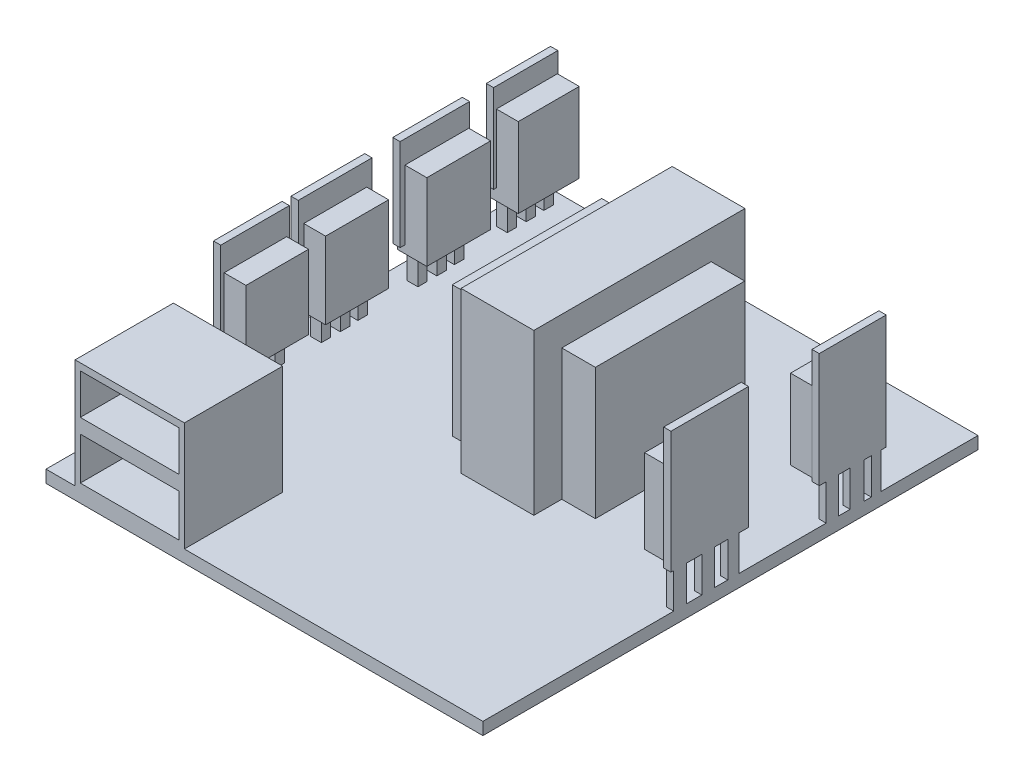
SolidWorks part; units mm, degrees
ref_plane "Front Plane" through (0, 0, 0) normal (0, 0, 1) x (1, 0, 0)
ref_plane "Top Plane" through (0, 0, 0) normal (0, 1, 0) x (1, 0, 0)
ref_plane "Right Plane" through (0, 0, 0) normal (1, 0, 0) x (0, 0, -1)
sketch "Sketch1" plane through (0, 0, 0) normal (0, 1, 0) x (1, 0, 0)
  line L1 (-32.4342, 13.5526) -> (27.5658, 13.5526)
  line L2 (-32.4342, 13.5526) -> (-32.4342, -54.4474)
  line L3 (-32.4342, -54.4474) -> (27.5658, -54.4474)
  line L4 (27.5658, 13.5526) -> (27.5658, -54.4474)
  dimension "D1" = 60
  dimension "D2" = 68
extrude "Boss-Extrude1" add sketch "Sketch1" along normal blind 1.7
sketch "Sketch2" plane through (0, 1.7, 0) normal (0, 1, 0) x (1, 0, 0)
  line L0 (27.5658, -54.4474) -> (27.5658, 13.5526) construction
  line L1 (-3.4342, 2.5526) -> (6.5658, 2.5526)
  line L2 (-3.4342, 2.5526) -> (-3.4342, -26.4474)
  line L3 (-3.4342, -26.4474) -> (6.5658, -26.4474)
  line L4 (6.5658, 2.5526) -> (6.5658, -26.4474)
  line L5 (-32.4342, -54.4474) -> (27.5658, -54.4474) construction
  dimension "D1" = 29
  dimension "D2" = 10
  dimension "D3" = 21
  dimension "D4" = 28
extrude "Boss-Extrude2" add sketch "Sketch2" along normal blind 22
sketch "Sketch3" plane through (0, 1.7, 0) normal (0, 1, 0) x (1, 0, 0)
  line L1 (-8.4662, -2.0985) -> (11.1829, -2.0985)
  line L2 (-8.4662, -2.0985) -> (-8.4662, -22.6146)
  line L3 (-8.4662, -22.6146) -> (11.1829, -22.6146)
  line L4 (11.1829, -2.0985) -> (11.1829, -22.6146)
extrude "Boss-Extrude3" add sketch "Sketch3" along normal blind 18
sketch "Sketch4" plane through (0, 1.7, 0) normal (0, 1, 0) x (1, 0, 0)
  line L0 (-32.4342, -54.4474) -> (27.5658, -54.4474) construction
  line L1 (-28.4342, -40.9474) -> (-13.4342, -40.9474)
  line L2 (-28.4342, -40.9474) -> (-28.4342, -54.4474)
  line L3 (-28.4342, -54.4474) -> (-13.4342, -54.4474)
  line L4 (-13.4342, -40.9474) -> (-13.4342, -54.4474)
  line L5 (-32.4342, 13.5526) -> (-32.4342, -54.4474) construction
  dimension "D1" = 15
  dimension "D2" = 13.5
  dimension "D3" = 4
extrude "Boss-Extrude4" add sketch "Sketch4" along normal blind 15
sketch "Sketch5" plane through (0, 0, 54.4474) normal (0, 0, 1) x (1, 0, 0)
  line L1 (-27.7262, 15.7476) -> (-14.1813, 15.7476)
  line L2 (-27.7262, 15.7476) -> (-27.7262, 10.2076)
  line L3 (-27.7262, 10.2076) -> (-14.1813, 10.2076)
  line L4 (-14.1813, 15.7476) -> (-14.1813, 10.2076)
  line L5 (-27.7262, 8.2207) -> (-14.1813, 8.2207)
  line L6 (-27.7262, 8.2207) -> (-27.7262, 2.3932)
  line L7 (-27.7262, 2.3932) -> (-14.1813, 2.3932)
  line L8 (-14.1813, 8.2207) -> (-14.1813, 2.3932)
extrude "Cut-Extrude2" cut sketch "Sketch5" against normal blind 13
sketch "Sketch6" plane through (27.5658, 0, 0) normal (1, 0, 0) x (0, 0, -1)
  line L1 (-28.2345, 18.5486) -> (-18.4099, 18.5486)
  line L2 (-28.2345, 18.5486) -> (-28.2345, 7.0494)
  line L3 (-28.2345, 7.0494) -> (-18.4099, 7.0494)
  line L4 (-18.4099, 18.5486) -> (-18.4099, 7.0494)
  line L5 (-8.1946, 17.9904) -> (0.9043, 17.9904)
  line L6 (-8.1946, 17.9904) -> (-8.1946, 7.0494)
  line L7 (-8.1946, 7.0494) -> (0.9043, 7.0494)
  line L8 (0.9043, 17.9904) -> (0.9043, 7.0494)
extrude "Boss-Extrude5" add sketch "Sketch6" against normal blind 4 separate body
sketch "Sketch7" plane through (27.5658, 0, 0) normal (1, 0, 0) x (0, 0, -1)
  line L0 (-28.2345, 18.5486) -> (-28.2345, 7.0494) construction
  line L1 (-28.2345, 8.6124) -> (-26.4474, 8.6124)
  line L2 (-28.2345, 8.6124) -> (-28.2345, 1.7)
  line L3 (-28.2345, 1.7) -> (-26.4474, 1.7)
  line L4 (-26.4474, 8.6124) -> (-26.4474, 1.7)
  line L5 (-22.6146, 1.7) -> (-2.0985, 1.7) construction
  line L6 (-24.3828, 8.6124) -> (-22.6146, 8.6124)
  line L7 (-24.3828, 8.6124) -> (-24.3828, 1.7)
  line L8 (-24.3828, 1.7) -> (-22.6146, 1.7)
  line L9 (-22.6146, 8.6124) -> (-22.6146, 1.7)
  line L10 (-20.8102, 8.6124) -> (-19.303, 8.6124)
  line L11 (-20.8102, 8.6124) -> (-20.8102, 1.7)
  line L12 (-20.8102, 1.7) -> (-19.303, 1.7)
  line L13 (-19.303, 8.6124) -> (-19.303, 1.7)
  line L14 (-54.4474, 1.7) -> (13.5526, 1.7) construction
  line L15 (-7.3014, 8.1658) -> (-5.6268, 8.1658)
  line L16 (-7.3014, 8.1658) -> (-7.3014, 1.7)
  line L17 (-7.3014, 1.7) -> (-5.6268, 1.7)
  line L18 (-5.6268, 8.1658) -> (-5.6268, 1.7)
  line L19 (-4.008, 8.1658) -> (-2.0985, 8.1658)
  line L20 (-4.008, 8.1658) -> (-4.008, 1.7)
  line L21 (-4.008, 1.7) -> (-2.0985, 1.7)
  line L22 (-2.0985, 8.1658) -> (-2.0985, 1.7)
  line L23 (-2.0985, 1.7) -> (2.5526, 1.7) construction
  line L24 (-1.1052, 8.1658) -> (0.227, 8.1658)
  line L25 (-1.1052, 8.1658) -> (-1.1052, 1.7)
  line L26 (-1.1052, 1.7) -> (0.227, 1.7)
  line L27 (0.227, 8.1658) -> (0.227, 1.7)
extrude "Boss-Extrude6" add sketch "Sketch7" against normal blind 1
sketch "Sketch8" plane through (27.5658, 0, 0) normal (1, 0, 0) x (0, 0, -1)
  line L1 (-17.9644, 6.5308) -> (-28.6207, 6.5308)
  line L2 (-17.9644, 6.5308) -> (-17.9644, 23.2934)
  line L3 (-17.9644, 23.2934) -> (-28.6207, 23.2934)
  line L4 (-28.6207, 6.5308) -> (-28.6207, 23.2934)
  line L5 (0.939, 6.6234) -> (-8.2504, 6.6234)
  line L6 (0.939, 6.6234) -> (0.939, 22.3444)
  line L7 (0.939, 22.3444) -> (-8.2504, 22.3444)
  line L8 (-8.2504, 6.6234) -> (-8.2504, 22.3444)
  point P10 (-17.9644, 6.5308)
  point P11 (0, 0)
  point P12 (0.939, 6.6234)
extrude "Boss-Extrude7" add sketch "Sketch8" against normal blind 1
sketch "Sketch9" plane through (0, 1.7, 0) normal (0, 1, 0) x (1, 0, 0)
  line L0 (-30.0284, -0.7621) -> (-28.707, -0.7621)
  line L1 (-30.3316, 11.821) -> (-29.0103, 11.821)
  line L2 (-30.3316, 11.821) -> (-30.3316, 10.4996)
  line L3 (-30.3316, 10.4996) -> (-29.0103, 10.4996)
  line L4 (-29.0103, 11.821) -> (-29.0103, 10.4996)
  line L5 (-30.3981, 9.2559) -> (-28.881, 9.2559)
  line L6 (-30.3981, 9.2559) -> (-30.3981, 7.9556)
  line L7 (-30.3981, 7.9556) -> (-28.881, 7.9556)
  line L8 (-28.881, 9.2559) -> (-28.881, 7.9556)
  line L9 (-30.3981, 6.6247) -> (-28.881, 6.6247)
  line L10 (-30.3981, 6.6247) -> (-30.3981, 5.3549)
  line L11 (-30.3981, 5.3549) -> (-28.881, 5.3549)
  line L12 (-28.881, 6.6247) -> (-28.881, 5.3549)
  line L13 (-30.0284, -0.7621) -> (-30.0284, -2.0835)
  line L14 (-30.0284, -2.0835) -> (-28.707, -2.0835)
  line L15 (-28.707, -0.7621) -> (-28.707, -2.0835)
  line L16 (-30.0948, -3.3272) -> (-28.5778, -3.3272)
  line L17 (-30.0948, -3.3272) -> (-30.0948, -4.6275)
  line L18 (-30.0948, -4.6275) -> (-28.5778, -4.6275)
  line L19 (-28.5778, -3.3272) -> (-28.5778, -4.6275)
  line L20 (-30.0948, -5.9584) -> (-28.5778, -5.9584)
  line L21 (-30.0948, -5.9584) -> (-30.0948, -7.2281)
  line L22 (-30.0948, -7.2281) -> (-28.5778, -7.2281)
  line L23 (-28.5778, -5.9584) -> (-28.5778, -7.2281)
  line L24 (-30.0181, -14.0318) -> (-28.6968, -14.0318)
  line L25 (-30.0181, -14.0318) -> (-30.0181, -15.3532)
  line L26 (-30.0181, -15.3532) -> (-28.6968, -15.3532)
  line L27 (-28.6968, -14.0318) -> (-28.6968, -15.3532)
  line L28 (-30.0846, -16.5969) -> (-28.5675, -16.5969)
  line L29 (-30.0846, -16.5969) -> (-30.0846, -17.8972)
  line L30 (-30.0846, -17.8972) -> (-28.5675, -17.8972)
  line L31 (-28.5675, -16.5969) -> (-28.5675, -17.8972)
  line L32 (-30.0846, -19.2281) -> (-28.5675, -19.2281)
  line L33 (-30.0846, -19.2281) -> (-30.0846, -20.4979)
  line L34 (-30.0846, -20.4979) -> (-28.5675, -20.4979)
  line L35 (-28.5675, -19.2281) -> (-28.5675, -20.4979)
  line L36 (-30.004, -25.4192) -> (-28.6827, -25.4192)
  line L37 (-30.004, -25.4192) -> (-30.004, -26.7406)
  line L38 (-30.004, -26.7406) -> (-28.6827, -26.7406)
  line L39 (-28.6827, -25.4192) -> (-28.6827, -26.7406)
  line L40 (-30.0705, -27.9843) -> (-28.5535, -27.9843)
  line L41 (-30.0705, -27.9843) -> (-30.0705, -29.2846)
  line L42 (-30.0705, -29.2846) -> (-28.5535, -29.2846)
  line L43 (-28.5535, -27.9843) -> (-28.5535, -29.2846)
  line L44 (-30.0705, -30.6155) -> (-28.5535, -30.6155)
  line L45 (-30.0705, -30.6155) -> (-30.0705, -31.8853)
  line L46 (-30.0705, -31.8853) -> (-28.5535, -31.8853)
  line L47 (-28.5535, -30.6155) -> (-28.5535, -31.8853)
extrude "Boss-Extrude8" add sketch "Sketch9" along normal blind 12
sketch "Sketch10" plane through (-30.3316, 0, 0) normal (-1, 0, 0) x (0, 0, 1)
  line L1 (-12.6827, 16.7065) -> (-4.3094, 16.7065)
  line L2 (-12.6827, 16.7065) -> (-12.6827, 5.7655)
  line L3 (-12.6827, 5.7655) -> (-4.3094, 5.7655)
  line L4 (-4.3094, 16.7065) -> (-4.3094, 5.7655)
  line L5 (-0.5136, 16.3157) -> (8.2504, 16.3157)
  line L6 (-0.5136, 16.3157) -> (-0.5136, 5.7655)
  line L7 (-0.5136, 5.7655) -> (8.2504, 5.7655)
  line L8 (8.2504, 16.3157) -> (8.2504, 5.7655)
  line L9 (13.4976, 16.3157) -> (22.1499, 16.3157)
  line L10 (13.4976, 16.3157) -> (13.4976, 5.7655)
  line L11 (13.4976, 5.7655) -> (22.1499, 5.7655)
  line L12 (22.1499, 16.3157) -> (22.1499, 5.7655)
  line L13 (24.4944, 15.925) -> (33.0909, 15.925)
  line L14 (24.4944, 15.925) -> (24.4944, 5.7655)
  line L15 (24.4944, 5.7655) -> (33.0909, 5.7655)
  line L16 (33.0909, 15.925) -> (33.0909, 5.7655)
extrude "Boss-Extrude9" add sketch "Sketch10" against normal blind 4
sketch "Sketch11" plane through (-30.3316, 0, 0) normal (-1, 0, 0) x (0, 0, 1)
  line L1 (-12.7385, 19.4417) -> (-3.9187, 19.4417)
  line L2 (-12.7385, 19.4417) -> (-12.7385, 7.3285)
  line L3 (-12.7385, 7.3285) -> (-3.9187, 7.3285)
  line L4 (-3.9187, 19.4417) -> (-3.9187, 7.3285)
  line L5 (-0.6252, 19.4417) -> (8.9202, 19.4417)
  line L6 (-0.6252, 19.4417) -> (-0.6252, 6.8261)
  line L7 (-0.6252, 6.8261) -> (8.9202, 6.8261)
  line L8 (8.9202, 19.4417) -> (8.9202, 6.8261)
  line L9 (12.7719, 19.4417) -> (22.9013, 19.4417)
  line L10 (12.7719, 19.4417) -> (12.7719, 7.3285)
  line L11 (12.7719, 7.3285) -> (22.9013, 7.3285)
  line L12 (22.9013, 19.4417) -> (22.9013, 7.3285)
  line L13 (24.13, 19.4417) -> (33.5531, 19.4417)
  line L14 (24.13, 19.4417) -> (24.13, 7.5829)
  line L15 (24.13, 7.5829) -> (33.5531, 7.5829)
  line L16 (33.5531, 19.4417) -> (33.5531, 7.5829)
extrude "Boss-Extrude10" add sketch "Sketch11" against normal blind 1
